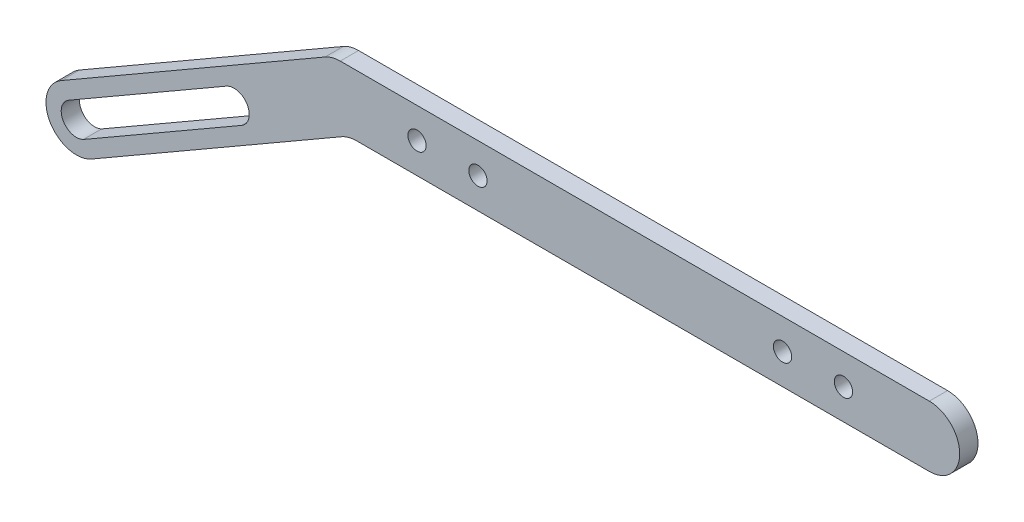
SolidWorks part; units mm, degrees
ref_plane "前视基准面" through (0, 0, 0) normal (0, 0, 1) x (1, 0, 0)
ref_plane "上视基准面" through (0, 0, 0) normal (0, 1, 0) x (1, 0, 0)
ref_plane "右视基准面" through (0, 0, 0) normal (1, 0, 0) x (0, 0, -1)
sketch "草图1" plane through (0, 0, 0) normal (0, 0, 1) x (1, 0, 0)
  line L0 (-57.217, 0) -> (42.783, 0) construction
  line L1 (-53.9031, 5) -> (42.783, 5)
  line L2 (-51.2236, -5) -> (42.783, -5)
  line L3 (-53.7236, -5.6699) -> (-94.717, -29.3374)
  line L4 (-56.4031, 4.3301) -> (-99.717, -20.6772)
  line L5 (-95.967, -27.1724) -> (-69.9862, -12.1724)
  line L6 (-98.467, -22.8422) -> (-72.4862, -7.8422)
  arc A0 (-94.717, -29.3374) -> (-99.717, -20.6772) centre (-97.217, -25.0073) cw
  arc A1 (42.783, -5) -> (42.783, 5) centre (42.783, 0) ccw
  arc A2 (-51.2236, -5) -> (-53.7236, -5.6699) centre (-51.2236, -10) ccw
  arc A3 (-53.9031, 5) -> (-56.4031, 4.3301) centre (-53.9031, 0) ccw
  arc A4 (-98.467, -22.8422) -> (-95.967, -27.1724) centre (-97.217, -25.0073) ccw
  arc A5 (-69.9862, -12.1724) -> (-72.4862, -7.8422) centre (-71.2362, -10.0073) ccw
  point P3 (-2.2989, 0)
  point P14 (-97.0901, -28.6748)
  point P15 (-94.717, -29.3374)
  dimension "D2" = 5
  dimension "D4" = 5
  dimension "D5" = 5
  dimension "D6" = 5
  dimension "D1" = 100
  dimension "D3" = 150
  dimension "D7" = 40
  dimension "D8" = 10
  dimension "D9" = 180
  dimension "D10" = 30
  dimension "D11" = 30
extrude "凸台-拉伸1" add sketch "草图1" along normal blind 3 contours L4 A0 L3 A2 L2 A1 L1 A3
sketch "草图2" plane through (0, 0, 3) normal (0, 0, 1) x (1, 0, 0)
  line L1 (-98.3347, -22.7711) -> (-72.5981, -7.912)
  line L2 (-96.0834, -27.2355) -> (-70.0986, -12.2425)
  line L4 (-56.4031, 4.3301) -> (-99.717, -20.6772) construction
  arc A0 (-98.3347, -22.7711) -> (-96.0834, -27.2355) centre (-97.217, -25.0073) ccw
  arc A1 (-99.717, -20.6772) -> (-94.717, -29.3374) centre (-97.217, -25.0073) ccw construction
  arc A2 (-72.5981, -7.912) -> (-70.0986, -12.2425) centre (-71.3481, -10.0771) cw
  point P1 (-98.5181, -22.8726)
  point P12 (-95.9277, -27.1492)
  dimension "D1" = 5
  dimension "D3" = 30
  dimension "D4" = 2.5
  dimension "D2" = 0
extrude "切除-拉伸1" cut sketch "草图2" against normal blind 3
sketch "草图3" plane through (0, 0, 3) normal (0, 0, 1) x (1, 0, 0)
  line L0 (-53.9031, 5) -> (42.783, 5) construction
  circle A0 centre (-31.3036, 0) radius 1.5
  circle A1 centre (-41.3036, 0) radius 1.5
  dimension "D1" = 3
  dimension "D2" = 3
  dimension "D3" = 10
  dimension "D4" = 5
extrude "切除-拉伸2" cut sketch "草图3" against normal blind 3
sketch "草图4" plane through (0, 0, 0) normal (0, 0, -1) x (-1, 0, 0)
  circle A0 centre (-18.6964, 0) radius 1.5 construction
  circle A1 centre (-28.6964, 0) radius 1.5 construction
  circle A2 centre (-18.6964, 0) radius 1.5
  circle A3 centre (-28.6964, 0) radius 1.5
extrude "切除-拉伸3" cut sketch "草图4" against normal through all
